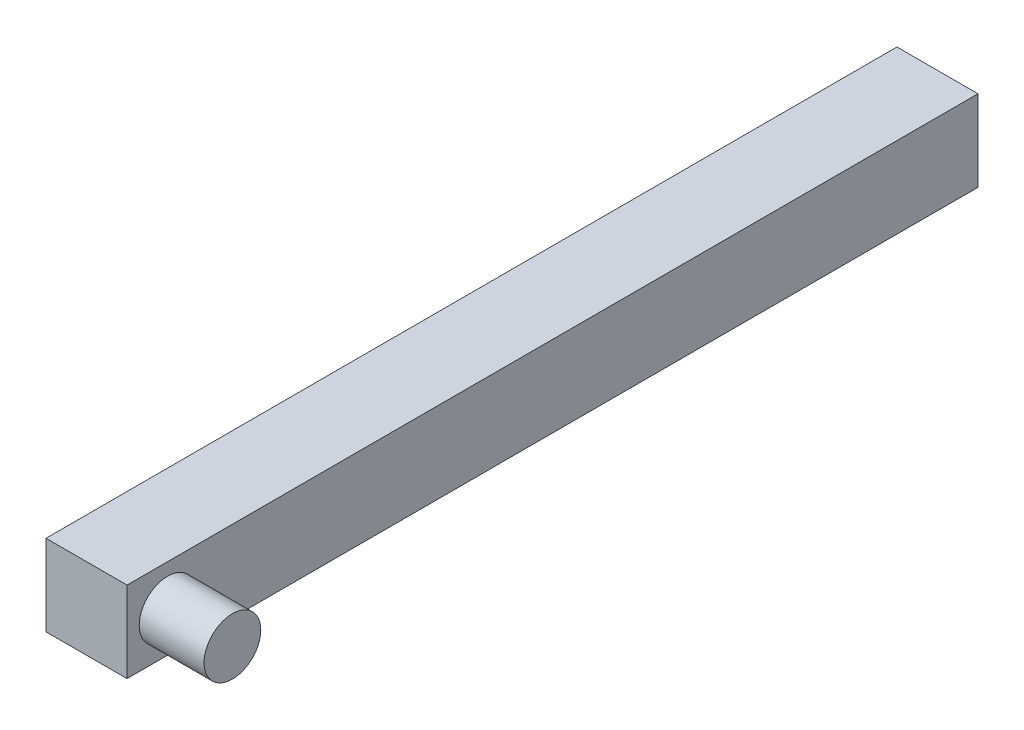
SolidWorks part; units mm, degrees
ref_plane "Front Plane" through (0, 0, 0) normal (0, 0, 1) x (1, 0, 0)
ref_plane "Top Plane" through (0, 0, 0) normal (0, 1, 0) x (1, 0, 0)
ref_plane "Right Plane" through (0, 0, 0) normal (1, 0, 0) x (0, 0, -1)
sketch "Sketch1" plane through (0, 0, 0) normal (0, 0, 1) x (1, 0, 0)
  line L5 (0, 0) -> (10, 0)
  line L6 (0, 0) -> (0, -10)
  line L7 (0, -10) -> (10, -10)
  line L8 (10, 0) -> (10, -10)
  dimension "D1" = 10
  dimension "D2" = 10
extrude "Boss-Extrude1" add sketch "Sketch1" along normal blind 205
sketch "Sketch2" plane through (10, 0, 0) normal (1, 0, 0) x (0, 0, -1)
  line L0 (-205, -10) -> (-205, 0) construction
  circle A2 centre (-200, -5.054) radius 3.5
  dimension "D2" = 7
  dimension "D1" = 5
extrude "Boss-Extrude2" add sketch "Sketch2" along normal blind 8
sketch "Sketch4" plane through (0, 0, 0) normal (0, 0, -1) x (-1, 0, 0)
  line L1 (-10, 0) -> (0, 0)
  line L2 (-10, 0) -> (-10, -10)
  line L3 (-10, -10) -> (0, -10)
  line L4 (0, 0) -> (0, -10)
extrude "Cut-Extrude1" cut sketch "Sketch4" against normal blind 100
